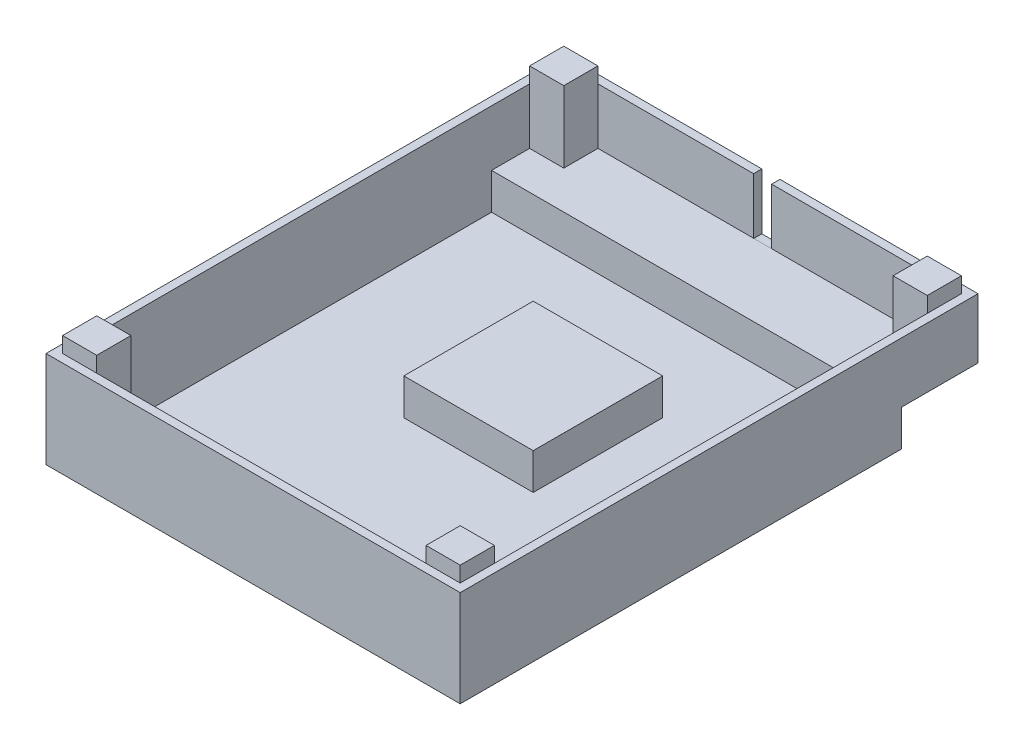
SolidWorks part; units mm, degrees
ref_plane "Front Plane" through (0, 0, 0) normal (0, 0, 1) x (1, 0, 0)
ref_plane "Top Plane" through (0, 0, 0) normal (0, 1, 0) x (1, 0, 0)
ref_plane "Right Plane" through (0, 0, 0) normal (1, 0, 0) x (0, 0, -1)
sketch "Sketch5" plane through (0, 0, 0) normal (1, 0, 0) x (0, 0, -1)
  line L1 (0, 0) -> (100, 0)
  line L2 (0, 0) -> (0, 11.6)
  line L3 (0, 11.6) -> (100, 11.6)
  line L4 (100, 0) -> (100, 11.6)
  dimension "D1" = 11.6
  dimension "D2" = 100
extrude "Boss-Extrude3" add sketch "Sketch5" along normal blind 80
sketch "Sketch6" plane through (80, 0, 0) normal (1, 0, 0) x (0, 0, -1)
  line L0 (100, 0) -> (100, 11.6) construction
  line L1 (0, 0) -> (85.25, 0)
  line L2 (0, 0) -> (0, -7)
  line L3 (0, -7) -> (85.25, -7)
  line L4 (85.25, 0) -> (85.25, -7)
  dimension "D1" = 7
  dimension "D2" = 14.75
extrude "Boss-Extrude4" add sketch "Sketch6" against normal up to vertex (80 mm away) separate body
sketch "Sketch7" plane through (0, 11.6, 0) normal (0, 1, 0) x (1, 0, 0)
  line L0 (80, 100) -> (0, 100) construction
  line L1 (1.6, 98.4) -> (78.4, 98.4)
  line L2 (1.6, 98.4) -> (1.6, 1.6)
  line L3 (1.6, 1.6) -> (78.4, 1.6)
  line L4 (78.4, 98.4) -> (78.4, 1.6)
  line L5 (0, 100) -> (0, 0) construction
  line L6 (80, 100) -> (80, 0) construction
  line L7 (80, 0) -> (0, 0) construction
  dimension "D1" = 1.6
  dimension "D2" = 1.6
  dimension "D3" = 1.6
  dimension "D4" = 1.6
extrude "Cut-Extrude1" cut sketch "Sketch7" against normal blind 10.8
sketch "Sketch8" plane through (0, 0.8, 0) normal (0, 1, 0) x (1, 0, 0)
  line L0 (1.6, 98.4) -> (1.6, 1.6) construction
  line L5 (1.6, 84.45) -> (78.4, 84.45)
  line L6 (1.6, 84.45) -> (1.6, 1.6)
  line L7 (1.6, 1.6) -> (78.4, 1.6)
  line L8 (78.4, 84.45) -> (78.4, 1.6)
  line L9 (0, 85.25) -> (80, 85.25) construction
  dimension "D1" = 0.8
extrude "Cut-Extrude2" cut sketch "Sketch8" against normal blind 7
sketch "Sketch10" plane through (0, -6.2, 0) normal (0, 1, 0) x (1, 0, 0)
  line L2 (1.6, 98.4) -> (1.6, 1.6) construction
  line L3 (1.6, 8.2) -> (8.2, 8.2)
  line L4 (1.6, 8.2) -> (1.6, 1.6)
  line L5 (1.6, 1.6) -> (8.2, 1.6)
  line L6 (8.2, 8.2) -> (8.2, 1.6)
  line L7 (1.6, 1.6) -> (78.4, 1.6) construction
  line L9 (78.4, 1.6) -> (71.8, 1.6)
  line L10 (78.4, 1.6) -> (78.4, 8.2)
  line L11 (78.4, 8.2) -> (71.8, 8.2)
  line L12 (71.8, 1.6) -> (71.8, 8.2)
  dimension "D1" = 6.6
  dimension "D3" = 6.6
  dimension "D4" = 6.6
  dimension "D2" = 6.6
extrude "Boss-Extrude5" add sketch "Sketch10" against normal up to surface (17.8 mm away)
sketch "Sketch12" plane through (0, 0.8, 0) normal (0, 1, 0) x (1, 0, 0)
  line L1 (1.6, 98.4) -> (8.2, 98.4)
  line L2 (1.6, 98.4) -> (1.6, 91.8)
  line L3 (1.6, 91.8) -> (8.2, 91.8)
  line L4 (8.2, 98.4) -> (8.2, 91.8)
  line L5 (78.4, 98.4) -> (71.8, 98.4)
  line L6 (78.4, 98.4) -> (78.4, 91.8)
  line L7 (78.4, 91.8) -> (71.8, 91.8)
  line L8 (71.8, 98.4) -> (71.8, 91.8)
  dimension "D1" = 6.6
  dimension "D2" = 6.6
  dimension "D3" = 6.6
  dimension "D4" = 6.6
extrude "Boss-Extrude6" add sketch "Sketch12" along normal up to surface (10.8 mm away) up to face at (40, 11.6, -29.1)
sketch "Sketch15" plane through (0, 0, -100) normal (0, 0, -1) x (-1, 0, 0)
  line L0 (-80, 11.6) -> (0, 11.6) construction
  line L1 (-41.75, 11.6) -> (-38.25, 11.6)
  line L2 (-41.75, 11.6) -> (-41.75, 0.7414)
  line L3 (-41.75, 0.7414) -> (-38.25, 0.7414)
  line L4 (-38.25, 11.6) -> (-38.25, 0.7414)
  line L6 (-80, 0) -> (-80, 11.6) construction
  dimension "D1" = 3.5
  dimension "D2" = 38.25
extrude "Cut-Extrude4" cut sketch "Sketch15" against normal up to surface (1.6 mm away) up to face at (40, 6.2, -98.4)
sketch "Sketch16" plane through (0, 11.6, 0) normal (0, 1, 0) x (1, 0, 0)
  line L0 (38.25, 100) -> (0, 100) construction
  line L1 (8.2, 91.8) -> (1.6, 91.8)
  line L2 (8.2, 91.8) -> (8.2, 98.4)
  line L3 (8.2, 98.4) -> (1.6, 98.4)
  line L4 (1.6, 91.8) -> (1.6, 98.4)
  line L5 (0, 100) -> (0, 0) construction
  line L6 (80, 100) -> (80, 0) construction
  line L12 (80, 0) -> (0, 0) construction
  line L13 (71.8, 8.2) -> (78.4, 8.2)
  line L14 (71.8, 8.2) -> (71.8, 1.6)
  line L15 (71.8, 1.6) -> (78.4, 1.6)
  line L16 (78.4, 8.2) -> (78.4, 1.6)
  line L18 (8.2, 8.2) -> (1.6, 8.2)
  line L19 (8.2, 8.2) -> (8.2, 1.6)
  line L20 (8.2, 1.6) -> (1.6, 1.6)
  line L21 (1.6, 8.2) -> (1.6, 1.6)
  line L23 (71.8, 98.4) -> (78.4, 98.4)
  line L24 (71.8, 98.4) -> (71.8, 91.8)
  line L25 (71.8, 91.8) -> (78.4, 91.8)
  line L26 (78.4, 98.4) -> (78.4, 91.8)
  dimension "D1" = 1.6
  dimension "D2" = 1.6
  dimension "D4" = 1.6
  dimension "D5" = 1.6
  dimension "D6" = 1.6
extrude "Boss-Extrude8" add sketch "Sketch16" along normal blind 3
sketch "Sketch18" plane through (0, -6.2, 0) normal (0, 1, 0) x (1, 0, 0)
  line L0 (1.6, 84.45) -> (1.6, 8.2) construction
  line L1 (27.5, 66.6) -> (52.5, 66.6)
  line L2 (27.5, 66.6) -> (27.5, 41.6)
  line L3 (27.5, 41.6) -> (52.5, 41.6)
  line L4 (52.5, 66.6) -> (52.5, 41.6)
  line L5 (8.2, 1.6) -> (71.8, 1.6) construction
  dimension "D1" = 25
  dimension "D2" = 25
  dimension "D3" = 25.9
  dimension "D4" = 40
extrude "Boss-Extrude9" add sketch "Sketch18" along normal blind 7
sketch "Sketch19" plane through (0, -7, 0) normal (0, -1, 0) x (1, 0, 0)
  line L0 (0, 0) -> (80, 0) construction
  line L1 (32.5, -43.6) -> (37, -43.6)
  line L2 (32.5, -43.6) -> (32.5, -49.6)
  line L3 (32.5, -49.6) -> (37, -49.6)
  line L4 (37, -43.6) -> (37, -49.6)
  line L5 (32.5, -58.6) -> (37, -58.6)
  line L6 (32.5, -58.6) -> (32.5, -64.6)
  line L7 (32.5, -64.6) -> (37, -64.6)
  line L8 (37, -58.6) -> (37, -64.6)
  line L9 (48, -51.35) -> (42, -51.35)
  line L10 (48, -51.35) -> (48, -56.85)
  line L11 (48, -56.85) -> (42, -56.85)
  line L12 (42, -51.35) -> (42, -56.85)
  line L13 (80, 0) -> (80, -85.25) construction
  dimension "D1" = 43.6
  dimension "D2" = 6
  dimension "D3" = 4.5
  dimension "D4" = 43
  dimension "D5" = 64.6
  dimension "D6" = 6
  dimension "D7" = 4.5
  dimension "D8" = 43
  dimension "D9" = 51.35
  dimension "D10" = 5.5
  dimension "D11" = 32
  dimension "D12" = 6
extrude "Cut-Extrude5" cut sketch "Sketch19" against normal offset from surface (6.2 mm away) 1.6 up to face at (40, 0.8, -54.1)
